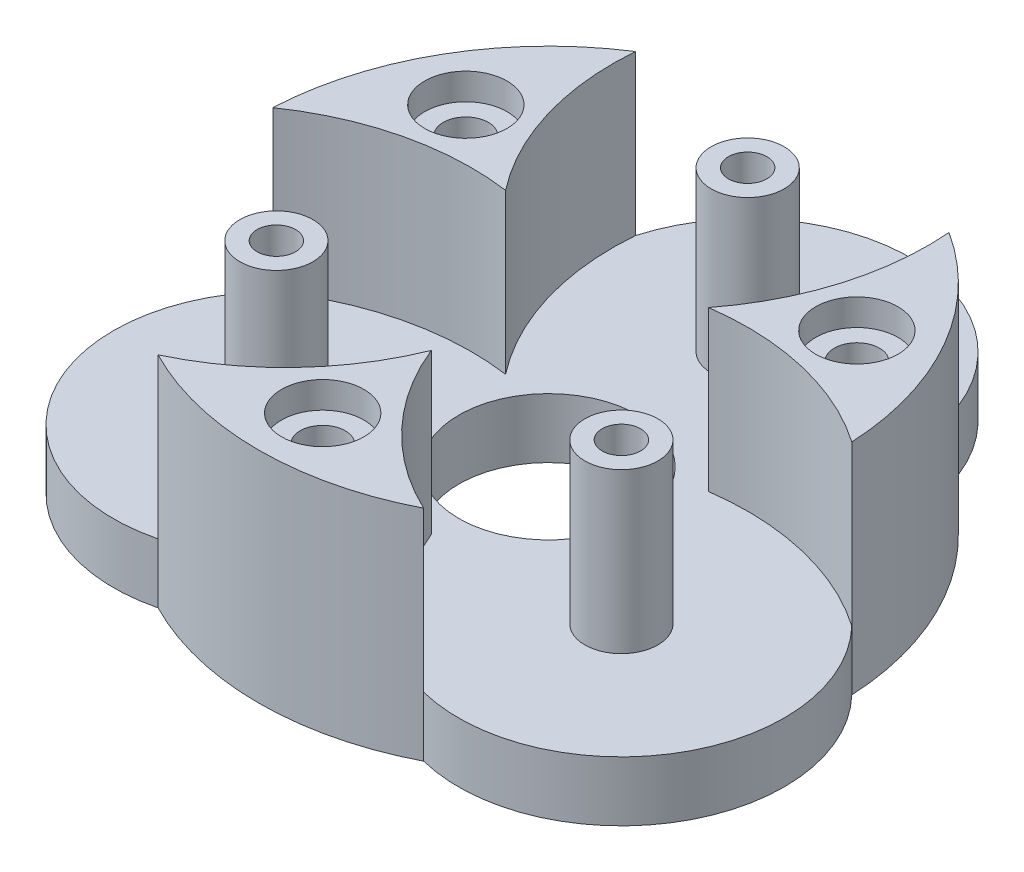
SolidWorks part; units mm, degrees
ref_plane "Alzado" through (0, 0, 0) normal (0, 0, 1) x (1, 0, 0)
ref_plane "Planta" through (0, 0, 0) normal (0, 1, 0) x (1, 0, 0)
ref_plane "Vista lateral" through (0, 0, 0) normal (1, 0, 0) x (0, 0, -1)
sketch "Croquis1" plane through (0, 0, 0) normal (0, 1, 0) x (1, 0, 0)
  circle A0 centre (0, 0) radius 5 construction
  circle A1 centre (0, 15) radius 10 construction
  circle A2 centre (0, 0) radius 25 construction
  circle A7 centre (0, 0) radius 21.825
  point P24 (0, 0)
  dimension "D1" = 10
  dimension "D2" = 20
  dimension "D3" = 43.65
extrude "Saliente-Extruir1" add sketch "Croquis1" along normal blind 4.5
sketch "Croquis2" plane through (0, 4.5, 0) normal (0, 1, 0) x (1, 0, 0)
  circle A0 centre (0, 0) radius 15 construction
  circle A1 centre (0, 15) radius 2.75
  circle A2 centre (12.9904, -7.5) radius 2.75
  circle A3 centre (-12.9904, -7.5) radius 2.75
  point P12 (0, 0)
  dimension "D1" = 30
  dimension "D2" = 5.5
  dimension "D3" = 3
extrude "Saliente-Extruir2" add sketch "Croquis2" along normal blind 12
hole_wizard "Taladro de margen para M121" positions "Croquis3" profile "Croquis4" hole size "M12" standard "ISO" end condition through all
sketch "Croquis3" plane through (0, 4.5, 0) normal (0, 1, 0) x (1, 0, 0)
  point P0 (0, 0)
sketch "Croquis4" plane through (0, 4.5, 0) normal (1, 0, 0) x (0, 0, 1)
  line L0 (0, 0) -> (0, 4.5)
  line L1 (0, 4.5) -> (6.75, 4.5)
  line L2 (6.75, 4.5) -> (6.75, 0)
  line L5 (6.75, 0) -> (0, 0)
  line L11 (0, -6.35) -> (0, 107.95) construction
  dimension "Diámetro de taladro hasta el siguiente" = 13.5
  dimension "Profundidad de taladro hasta el siguiente" = 4.5
sketch "Croquis5" plane through (0, 4.5, 0) normal (0, 1, 0) x (1, 0, 0)
  line L0 (0, 0) -> (-18.901, 10.9125) construction
  line L1 (-12.9904, -7.5) -> (0, 15) construction
  circle A0 centre (-12.9904, -7.5) radius 8.25 construction
  circle A1 centre (0, 15) radius 8.25 construction
  arc A4 (-7.6427, 4.4125) -> (-11.8002, 18.3599) centre (8.1271, 16.7067) cw
  arc A5 (-7.6427, 4.4125) -> (-21.8002, 1.0394) centre (-10.4048, -15.3916) ccw
  arc A6 (-11.8002, 18.3599) -> (-21.8002, 1.0394) centre (0, 0) ccw
  circle A7 centre (0, 0) radius 21.825 construction
  dimension "D1" = 20
  dimension "D2" = 13
extrude "Saliente-Extruir3" add sketch "Croquis5" along normal up to surface (12 mm away) up to face at (-12.9904, 16.5, 10.25)
sketch "Croquis8" plane through (0, 16.5, 0) normal (0, 1, 0) x (1, 0, 0)
  line L0 (-7.6427, 4.4125) -> (-18.901, 10.9125) construction
  circle A1 centre (-14.7224, 8.5) radius 1.7
  circle A2 centre (0, 0) radius 15 construction
  arc A3 (-11.8002, 18.3599) -> (-21.8002, 1.0394) centre (0, 0) ccw construction
  circle A4 centre (0, 0) radius 17 construction
  dimension "D1" = 3.4
  dimension "D2" = 2
extrude "Cortar-Extruir1" cut sketch "Croquis8" against normal up to surface (16.5 mm away) up to face at (0, 0, 6.75)
pattern_circular "MatrizC1" count 3 over 360 about axis through (0, 0, 0) along (0, 1, 0) of "Saliente-Extruir3", "Cortar-Extruir1"
hole_wizard "Taladro de margen para M2.51" positions "Croquis9" profile "Croquis10" hole size "M2.5" standard "ISO" end condition through all
sketch "Croquis9" plane through (0, 16.5, 0) normal (0, 1, 0) x (1, 0, 0)
  point P0 (12.9904, -7.5)
  point P4 (-12.9904, -7.5)
  point P7 (0, 15)
sketch "Croquis10" plane through (12.9904, 16.5, 7.5) normal (1, 0, 0) x (0, 0, 1)
  line L0 (0, 0) -> (0, 16.5)
  line L1 (0, 16.5) -> (1.45, 16.5)
  line L2 (1.45, 16.5) -> (1.45, 0)
  line L5 (1.45, 0) -> (0, 0)
  line L11 (0, -6.35) -> (0, 107.95) construction
  dimension "Diámetro de taladro hasta el siguiente" = 2.9
  dimension "Profundidad de taladro hasta el siguiente" = 16.5
sketch "Croquis11" plane through (0, 0, 0) normal (0, -1, 0) x (1, 0, 0)
  arc A0 (-10, 19.3992) -> (-21.8002, -1.0394) centre (0, 0) ccw construction
  arc A1 (-10, 19.3992) -> (-21.8002, -1.0394) centre (0, 0) ccw
  arc A2 (-21.8002, -1.0394) -> (-10, 19.3992) centre (-12.9904, 7.5) cw
  circle A3 centre (-12.9904, 7.5) radius 1.45 construction
  circle A4 centre (-12.9904, 7.5) radius 1.45 construction
extrude "Saliente-Extruir5" add sketch "Croquis11" against normal up to surface (4.5 mm away) up to face at (0, 4.5, 6.75)
pattern_circular "MatrizC2" count 3 every 120 about axis through (0, 0, 0) along (0, 1, 0) of "Saliente-Extruir5"
sketch "Croquis12" plane through (0, 0, 0) normal (0, -1, 0) x (1, 0, 0)
  circle A0 centre (-12.9904, 7.5) radius 2.875
  circle A1 centre (12.9904, 7.5) radius 2.875
  circle A2 centre (0, -15) radius 2.875
  point P10 (0, 0)
  dimension "D1" = 5.75
  dimension "D2" = 3
extrude "Cortar-Extruir2" cut sketch "Croquis12" against normal blind 2.2
sketch "Croquis13" plane through (0, 16.5, 0) normal (0, 1, 0) x (1, 0, 0)
  circle A0 centre (0, -17) radius 3.1
  circle A2 centre (-14.7224, 8.5) radius 3.1
  circle A3 centre (14.7224, 8.5) radius 3.1
  point P11 (0, 0)
  dimension "D1" = 6.2
  dimension "D2" = 3
extrude "Cortar-Extruir3" cut sketch "Croquis13" against normal blind 2
